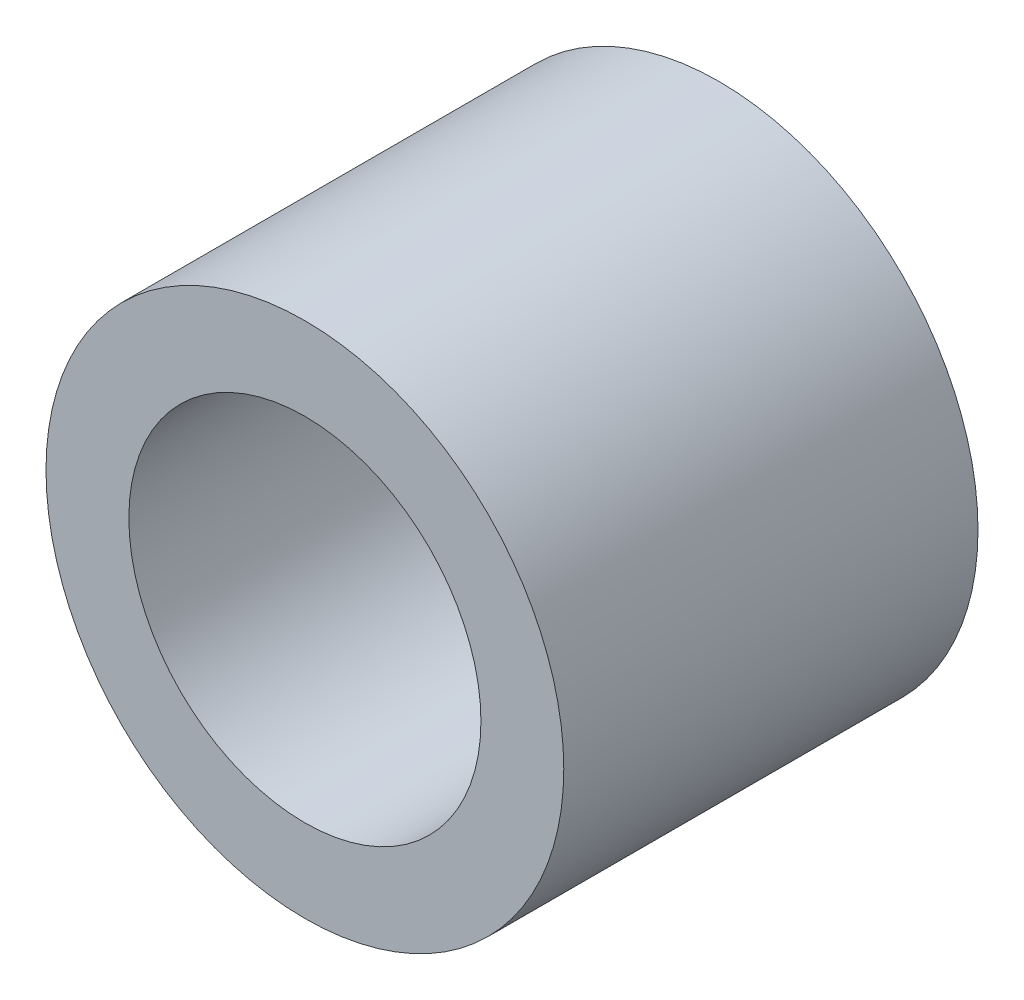
SolidWorks part; units mm, degrees
ref_plane "Front Plane" through (0, 0, 0) normal (0, 0, 1) x (1, 0, 0)
ref_plane "Top Plane" through (0, 0, 0) normal (0, 1, 0) x (1, 0, 0)
ref_plane "Right Plane" through (0, 0, 0) normal (1, 0, 0) x (0, 0, -1)
sketch "Sketch2" plane through (0, 0, 0) normal (0, 0, 1) x (1, 0, 0)
  circle A0 centre (-44.1446, 4.5788) radius 4.25
  circle A1 centre (-44.1446, 4.5788) radius 6.25
extrude "Boss-Extrude2" add sketch "Sketch2" along normal blind 10
